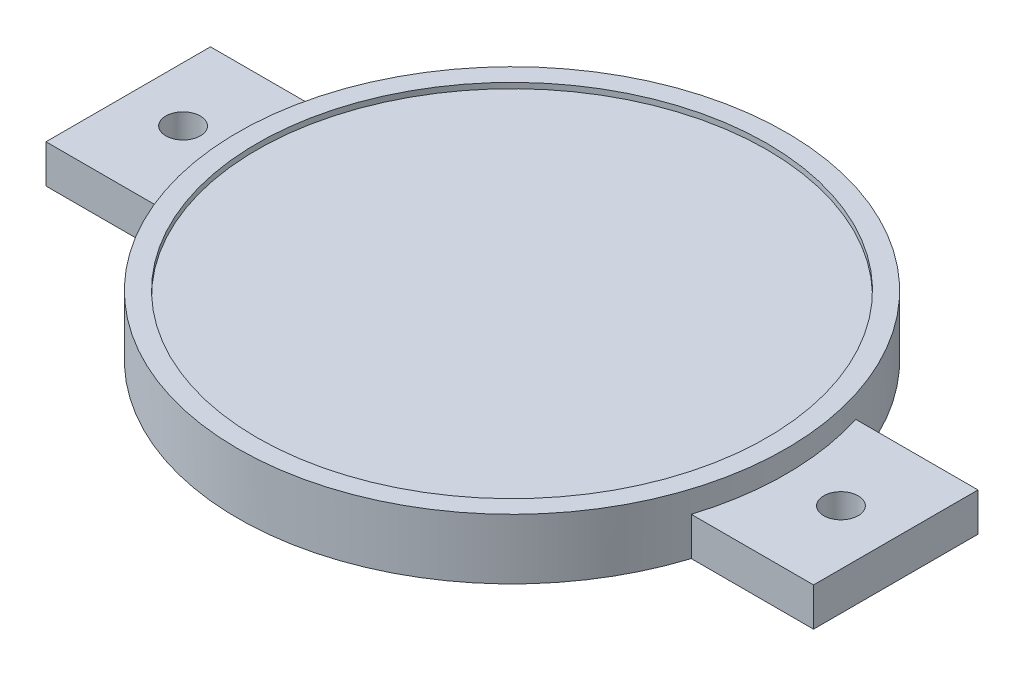
SolidWorks part; units mm, degrees
ref_plane "Front Plane" through (0, 0, 0) normal (0, 0, 1) x (1, 0, 0)
ref_plane "Top Plane" through (0, 0, 0) normal (0, 1, 0) x (1, 0, 0)
ref_plane "Right Plane" through (0, 0, 0) normal (1, 0, 0) x (0, 0, -1)
sketch "Sketch1" plane through (0, 0, 0) normal (0, 1, 0) x (1, 0, 0)
  circle A0 centre (0, 0) radius 50
  dimension "D1" = 100
extrude "Boss-Extrude1" add sketch "Sketch1" along normal blind 10
sketch "Sketch2" plane through (0, 10, 0) normal (0, 1, 0) x (1, 0, 0)
  circle A1 centre (0, 0) radius 46.5
  circle A2 centre (0, 0) radius 50
  circle A3 centre (0, 0) radius 50
  dimension "D2" = 93
  dimension "D1" = 0
extrude "Boss-Extrude2" add sketch "Sketch2" along normal blind 1
sketch "Sketch3" plane through (0, 0, 0) normal (0, -1, 0) x (1, 0, 0)
  circle A0 centre (0, 0) radius 47
  circle A1 centre (0, 0) radius 50 construction
  dimension "D1" = 3
extrude "Cut-Extrude1" cut sketch "Sketch3" against normal blind 7
sketch "Sketch4" plane through (0, 0, 0) normal (0, 1, 0) x (1, 0, 0)
  line L0 (-47.697, 15) -> (-70, 15)
  line L1 (-70, 15) -> (-70, -15)
  line L2 (-70, 0) -> (-50, 0) construction
  line L3 (0, 0) -> (0, 17.9128) construction
  line L4 (-47.697, -15) -> (-70, -15)
  line L5 (70, 0) -> (50, 0) construction
  line L6 (47.697, -15) -> (70, -15)
  line L7 (70, 15) -> (70, -15)
  line L8 (47.697, 15) -> (70, 15)
  arc A0 (-47.697, -15) -> (-47.697, 15) centre (0, 0) cw
  circle A1 centre (60, 0) radius 3.15
  circle A2 centre (0, 0) radius 50 construction
  circle A3 centre (-60, 0) radius 3.15
  arc A4 (47.697, -15) -> (47.697, 15) centre (0, 0) ccw
  dimension "D3" = 6.3
  dimension "D1" = 30
  dimension "D2" = 20
extrude "Boss-Extrude3" add sketch "Sketch4" along normal blind 7
